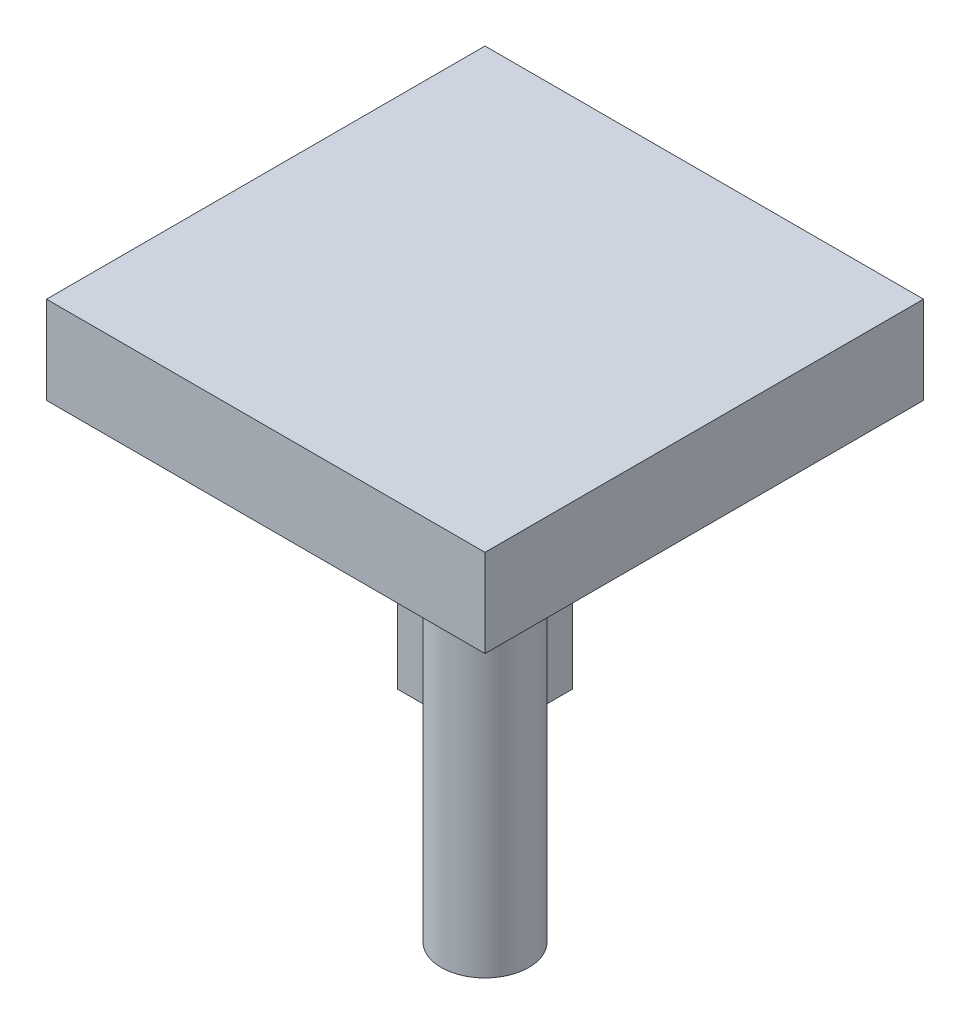
SolidWorks part; units mm, degrees
ref_plane "Front Plane" through (0, 0, 0) normal (0, 0, 1) x (1, 0, 0)
ref_plane "Top Plane" through (0, 0, 0) normal (0, 1, 0) x (1, 0, 0)
ref_plane "Right Plane" through (0, 0, 0) normal (1, 0, 0) x (0, 0, -1)
sketch "Sketch1" plane through (0, 0, 0) normal (0, 1, 0) x (1, 0, 0)
  line L1 (50, 50) -> (-50, 50)
  line L2 (50, 50) -> (50, -50)
  line L3 (50, -50) -> (-50, -50)
  line L4 (-50, 50) -> (-50, -50)
  line L5 (50, 50) -> (-50, -50) construction
  line L6 (50, -50) -> (-50, 50) construction
  point P0 (0, 0)
  dimension "D1" = 100
extrude "Boss-Extrude1" add sketch "Sketch1" along normal blind 20
sketch "Sketch2" plane through (0, 0, 0) normal (0, -1, 0) x (1, 0, 0)
  line L0 (50, 50) -> (0, 0) construction
  line L1 (0, 0) -> (-50, -50) construction
  line L3 (-35, -35) -> (-15, -35)
  line L4 (-35, -35) -> (-35, -15)
  line L5 (-35, -15) -> (-15, -15)
  line L6 (-15, -35) -> (-15, -15)
  line L7 (-35, -35) -> (-15, -15) construction
  line L8 (-35, -15) -> (-15, -35) construction
  circle A0 centre (25, 25) radius 10
  point P8 (-25, -25)
  dimension "D1" = 20
  dimension "D2" = 20
surface "Surface-Extrude1" sketch "Sketch2" parameters "D1"=80, "D19"=2
